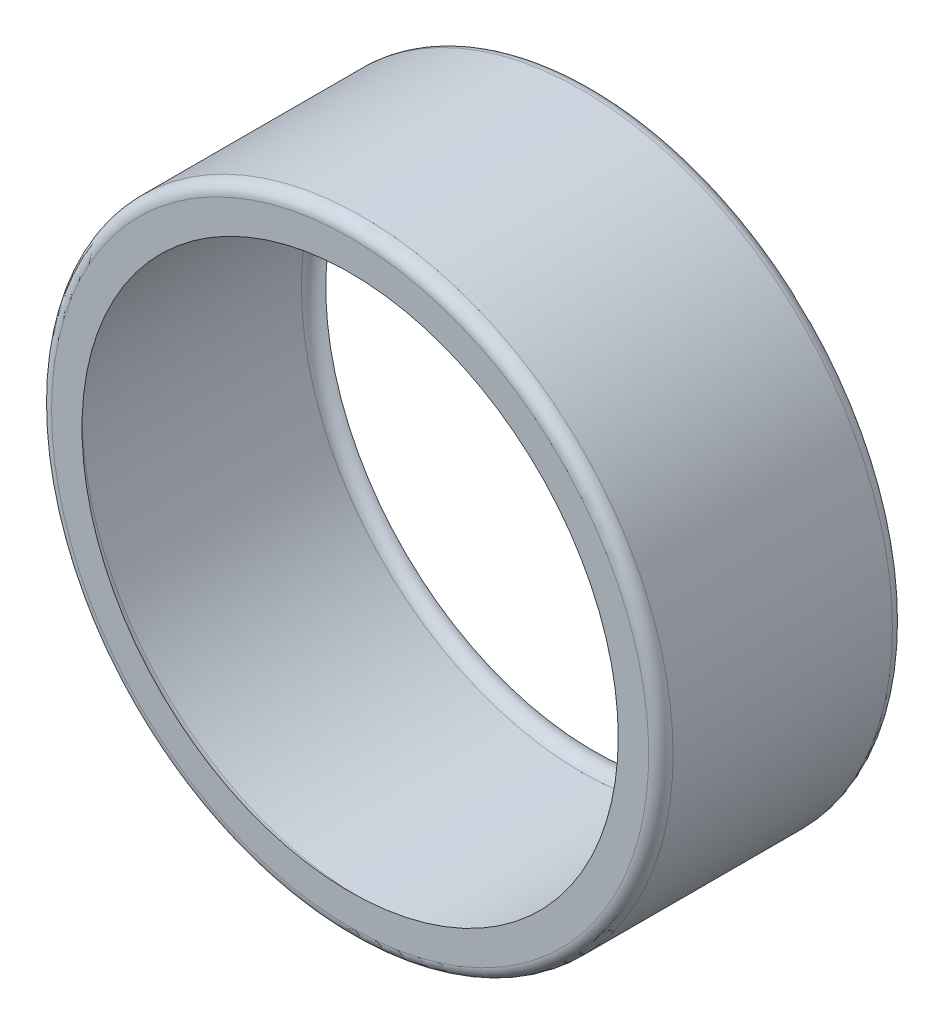
SolidWorks part; units mm, degrees
material "BUTYL"
ref_plane "Front Plane" through (0, 0, 0) normal (0, 0, 1) x (1, 0, 0)
ref_plane "Top Plane" through (0, 0, 0) normal (0, 1, 0) x (1, 0, 0)
ref_plane "Right Plane" through (0, 0, 0) normal (1, 0, 0) x (0, 0, -1)
sketch "Sketch1" plane through (0, 0, 0) normal (1, 0, 0) x (0, 0, -1)
  line L0 (0, 0) -> (14.4175, 0) construction
  line L1 (0, 27.94) -> (0, 32.385)
  line L2 (0, 32.385) -> (25.4, 32.385)
  line L3 (25.4, 32.385) -> (25.4, 27.94)
  line L4 (1.27, 29.21) -> (24.13, 29.21)
  arc A0 (0, 27.94) -> (1.27, 29.21) centre (1.27, 27.94) cw
  arc A1 (25.4, 27.94) -> (24.13, 29.21) centre (24.13, 27.94) ccw
  dimension "D1" = 1.27
  dimension "D2" = 64.77
  dimension "D3" = 58.42
  dimension "D4" = 25.4
revolve "Revolve1" add sketch "Sketch1" angle 360 about L0
fillet "Fillet1" radius 1.27 2 edges at (32.385, 0, -25.4) (32.385, 0, 0)
